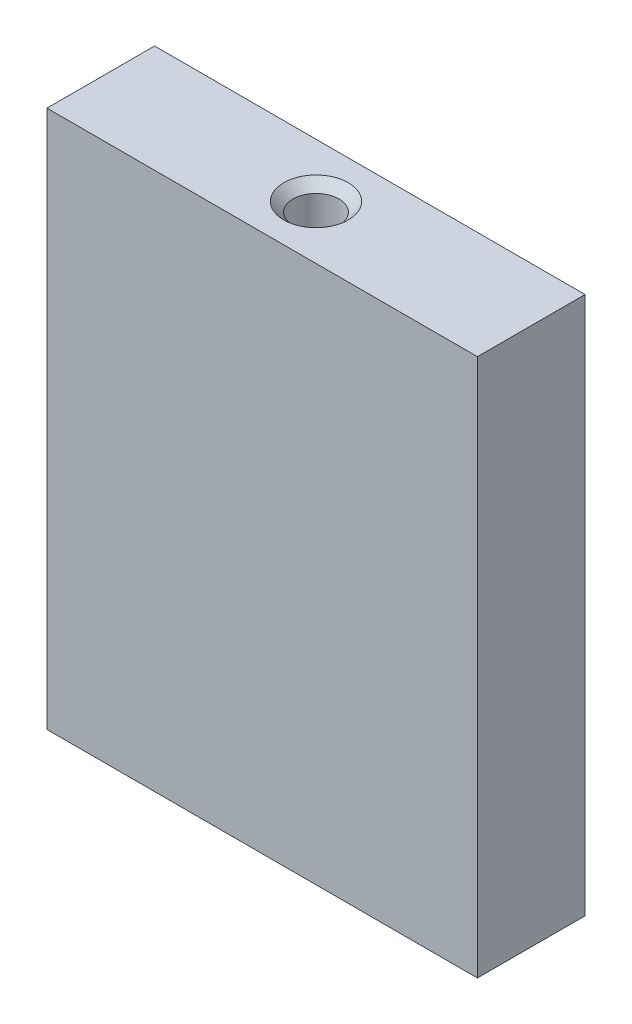
SolidWorks part; units mm, degrees
ref_plane "Front Plane" through (0, 0, 0) normal (0, 0, 1) x (1, 0, 0)
ref_plane "Top Plane" through (0, 0, 0) normal (0, 1, 0) x (1, 0, 0)
ref_plane "Right Plane" through (0, 0, 0) normal (1, 0, 0) x (0, 0, -1)
sketch "Sketch1" plane through (0, 0, 0) normal (0, 1, 0) x (1, 0, 0)
  line L1 (-25.4, -6.35) -> (25.4, -6.35)
  line L2 (-25.4, -6.35) -> (-25.4, 6.35)
  line L3 (-25.4, 6.35) -> (25.4, 6.35)
  line L4 (25.4, -6.35) -> (25.4, 6.35)
  line L5 (-25.4, -6.35) -> (25.4, 6.35) construction
  line L6 (-25.4, 6.35) -> (25.4, -6.35) construction
  point P0 (0, 0)
  dimension "D1" = 50.8
  dimension "D2" = 12.7
extrude "Boss-Extrude1" add sketch "Sketch1" along normal mid plane 63.5
sketch "Sketch2" plane through (0, 31.75, 0) normal (0, 1, 0) x (1, 0, 0)
  point P0 (0, 0)
hole_wizard "1/4-28 Tapped Hole1" positions "Sketch2" profile "Sketch3" tap size "1/4-28" standard "ANSI Inch"
sketch "Sketch3" plane through (0, 31.75, 0) normal (1, 0, 0) x (0, 0, 1)
  line L0 (0, 0) -> (0, 7.9754)
  line L1 (0, 7.9754) -> (2.7051, 6.35)
  line L2 (2.7051, 6.35) -> (2.7051, 1.1049)
  line L3 (2.7051, 1.1049) -> (3.81, 0)
  line L5 (3.81, 0) -> (0, 0)
  line L6 (-2.7051, 1.1049) -> (-3.81, 0) construction
  line L10 (0, 7.9754) -> (-2.7051, 6.35) construction
  line L11 (0, -6.35) -> (0, 107.95) construction
  dimension "Tap Drill Dia." = 5.4102
  dimension "Tap Drill Depth" = 6.35
  dimension "Near C'Sink Dia." = 7.62
  dimension "Near C'Sink Angle" = 90
  dimension "Drill Angle" = 118
cosmetic thread "Hole Thread1"
mirror "Mirror1" about plane through (0, 0, 0) normal (0, 1, 0) of "1/4-28 Tapped Hole1"
cosmetic thread "Hole Thread2"
